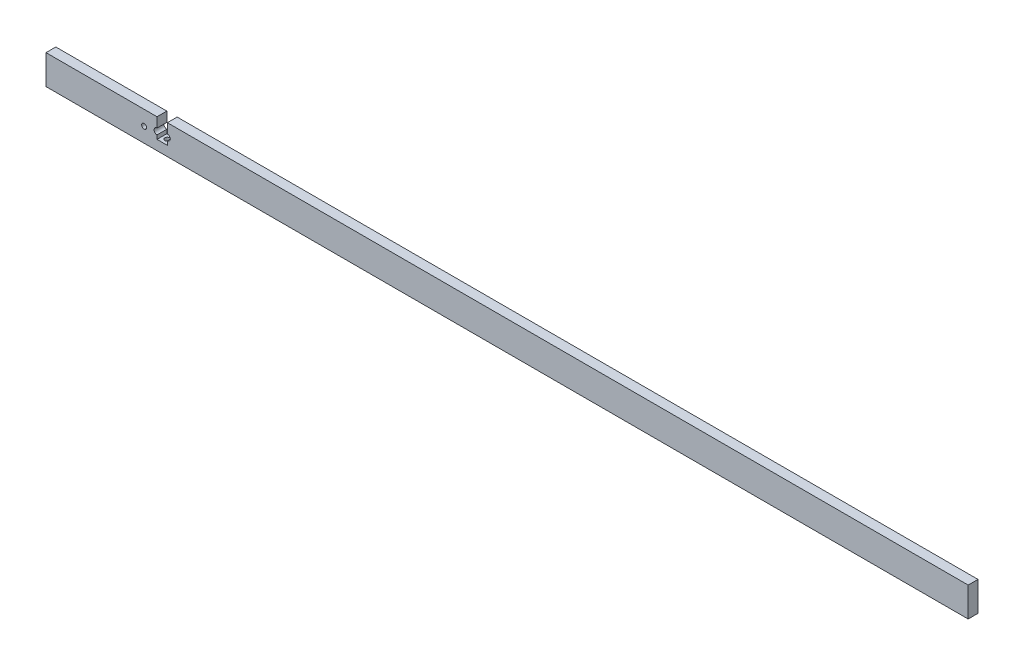
SolidWorks part; units mm, degrees
ref_plane "Plan de face" through (0, 0, 0) normal (0, 0, 1) x (1, 0, 0)
ref_plane "Plan de dessus" through (0, 0, 0) normal (0, 1, 0) x (1, 0, 0)
ref_plane "Plan de droite" through (0, 0, 0) normal (1, 0, 0) x (0, 0, -1)
sketch "Esquisse1" plane through (0, 0, 0) normal (0, 0, 1) x (1, 0, 0)
  line L1 (235, -7.5) -> (-235, -7.5)
  line L2 (235, -7.5) -> (235, 7.5)
  line L3 (235, 7.5) -> (-235, 7.5)
  line L4 (-235, -7.5) -> (-235, 7.5)
  line L5 (235, -7.5) -> (-235, 7.5) construction
  line L6 (235, 7.5) -> (-235, -7.5) construction
  point P0 (0, 0)
  dimension "D1" = 470
  dimension "D2" = 15
extrude "Boss.-Extru.1" add sketch "Esquisse1" along normal blind 5
sketch "Esquisse2" plane through (0, 0, 5) normal (0, 0, 1) x (1, 0, 0)
  circle A0 centre (-185, 0) radius 1.25
  dimension "D3" = 2.5
  dimension "D1" = 50
  dimension "D2" = 7.5
extrude "Enlèv. mat.-Extru.1" cut sketch "Esquisse2" against normal through all
sketch "Esquisse3" plane through (0, 0, 5) normal (0, 0, 1) x (1, 0, 0)
  line L0 (-178.41, 7.5) -> (-178.41, -2.5)
  line L1 (235, 7.5) -> (-235, 7.5) construction
  line L2 (-178.41, -2.5) -> (-173.16, -2.5)
  line L3 (-173.16, -2.5) -> (-173.16, 7.5)
  line L4 (-178.41, 7.5) -> (-173.16, 7.5)
  dimension "D1" = 5.25
  dimension "D2" = 10
extrude "Enlèv. mat.-Extru.2" cut sketch "Esquisse3" against normal through all
sketch "Esquisse4" plane through (0, -7.5, 0) normal (0, -1, 0) x (-1, 0, 0)
  circle A0 centre (175.91, -2.3127) radius 1.25
  dimension "D2" = 2.5
  dimension "D1" = 2.5
extrude "Enlèv. mat.-Extru.3" cut sketch "Esquisse4" against normal blind 10
sketch "Esquisse5" plane through (0, 0, 5) normal (0, 0, 1) x (1, 0, 0)
  line L0 (-173.16, -2.5) -> (-173.16, 7.5) construction
  line L1 (-178.41, 2.5) -> (-178.41, -0.5)
  line L2 (-173.16, 2.5) -> (-173.16, -0.5)
  line L3 (-178.41, 7.5) -> (-178.41, -2.5) construction
  arc A0 (-178.41, 2.5) -> (-178.41, -0.5) centre (-178.41, 1) ccw
  arc A1 (-173.16, 2.5) -> (-173.16, -0.5) centre (-173.16, 1) cw
  dimension "D1" = 1.5
  dimension "D3" = 1.5
  dimension "D2" = 2
  dimension "D4" = 2
  dimension "D5" = 0
  dimension "D6" = 0
  dimension "D7" = 0
extrude "Enlèv. mat.-Extru.4" cut sketch "Esquisse5" against normal blind 10
